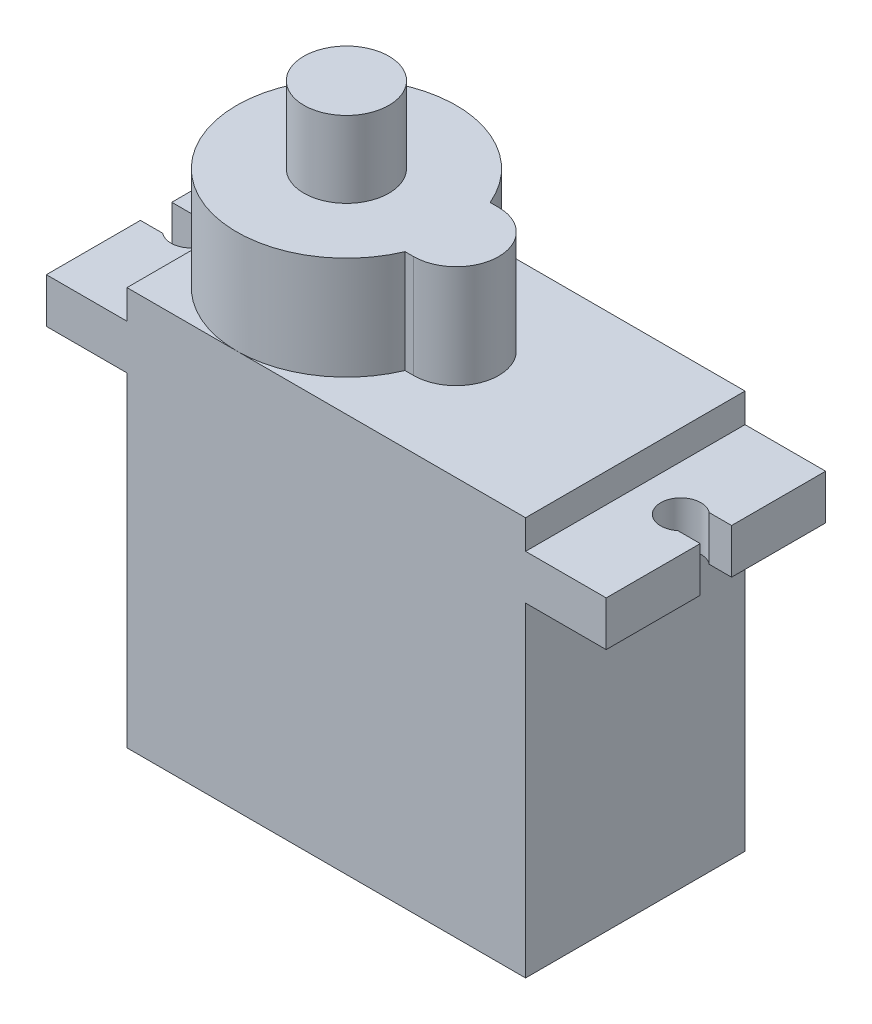
SolidWorks part; units mm, degrees
ref_plane "Front Plane" through (0, 0, 0) normal (0, 0, 1) x (1, 0, 0)
ref_plane "Top Plane" through (0, 0, 0) normal (0, 1, 0) x (1, 0, 0)
ref_plane "Right Plane" through (0, 0, 0) normal (1, 0, 0) x (0, 0, -1)
sketch "Sketch1" plane through (0, 0, 0) normal (0, 1, 0) x (1, 0, 0)
  line L1 (11.303, -6.223) -> (-11.303, -6.223)
  line L2 (11.303, -6.223) -> (11.303, 6.223)
  line L3 (11.303, 6.223) -> (-11.303, 6.223)
  line L4 (-11.303, -6.223) -> (-11.303, 6.223)
  line L5 (11.303, -6.223) -> (-11.303, 6.223) construction
  line L6 (11.303, 6.223) -> (-11.303, -6.223) construction
  point P0 (0, 0)
  dimension "D1" = 22.606
  dimension "D2" = 12.446
extrude "Boss-Extrude1" add sketch "Sketch1" along normal blind 18.415
sketch "Sketch2" plane through (0, 18.415, 0) normal (0, 1, 0) x (1, 0, 0)
  line L0 (0, 6.223) -> (-17.0969, 6.223) construction
  line L1 (11.303, 6.223) -> (-11.303, 6.223) construction
  line L2 (-11.303, 6.223) -> (-11.303, -6.223) construction
  line L3 (15.875, -6.223) -> (-15.875, -6.223)
  line L4 (15.875, -6.223) -> (15.875, 6.223) construction
  line L5 (15.875, 6.223) -> (-15.875, 6.223)
  line L6 (-15.875, -6.223) -> (-15.875, 6.223) construction
  line L7 (15.875, -6.223) -> (-15.875, 6.223) construction
  line L8 (15.875, 6.223) -> (-15.875, -6.223) construction
  line L9 (-15.875, 6.223) -> (-15.875, 0.889)
  line L10 (-15.875, 0.889) -> (-14.605, 0.889)
  line L11 (-15.875, 0) -> (-12.9515, 0) construction
  line L12 (-15.875, -0.889) -> (-14.605, -0.889)
  line L13 (-15.875, -6.223) -> (-15.875, -0.889)
  line L14 (0, 0) -> (0, 6.223) construction
  line L15 (15.875, -6.223) -> (15.875, -0.889)
  line L16 (15.875, -0.889) -> (14.605, -0.889)
  line L17 (15.875, 0.889) -> (14.605, 0.889)
  line L18 (15.875, 6.223) -> (15.875, 0.889)
  circle A0 centre (-13.8866, 0) radius 1.143 construction
  arc A1 (-14.605, 0.889) -> (-14.605, -0.889) centre (-13.8866, 0) cw
  arc A2 (14.605, 0.889) -> (14.605, -0.889) centre (13.8866, 0) ccw
  point P4 (0, 0)
  dimension "D4" = 2.286
  dimension "D1" = 4.572
  dimension "D2" = 5.334
  dimension "D3" = 1.27
extrude "Boss-Extrude2" add sketch "Sketch2" along normal blind 2.54
sketch "Sketch3" plane through (0, 20.955, 0) normal (0, 1, 0) x (1, 0, 0)
  line L0 (15.875, 6.223) -> (-15.875, 6.223) construction
  line L1 (11.303, -6.223) -> (-11.303, -6.223)
  line L2 (11.303, -6.223) -> (11.303, 6.223)
  line L3 (11.303, 6.223) -> (-11.303, 6.223)
  line L4 (-11.303, -6.223) -> (-11.303, 6.223)
  line L5 (11.303, -6.223) -> (-11.303, 6.223) construction
  line L6 (11.303, 6.223) -> (-11.303, -6.223) construction
  point P0 (0, 0)
  dimension "D1" = 22.606
extrude "Boss-Extrude3" add sketch "Sketch3" along normal blind 1.651
sketch "Sketch4" plane through (0, 22.606, 0) normal (0, 1, 0) x (1, 0, 0)
  line L0 (-5.08, -6.223) -> (-5.08, 0) construction
  line L1 (-11.303, -6.223) -> (11.303, -6.223) construction
  line L2 (-5.08, 0) -> (-11.303, 0) construction
  line L3 (-11.303, 6.223) -> (-11.303, -6.223) construction
  line L4 (1.143, 2.413) -> (0.6561, 2.413)
  line L5 (1.143, -2.413) -> (0.6561, -2.413)
  circle A0 centre (-5.08, 0) radius 6.223 construction
  circle A1 centre (1.143, 0) radius 2.413 construction
  arc A2 (0.6561, 2.413) -> (-11.303, 0) centre (-5.08, 0) ccw
  arc A3 (1.143, -2.413) -> (1.143, 2.413) centre (1.143, 0) ccw
  arc A4 (0.6561, -2.413) -> (-11.303, 0) centre (-5.08, 0) cw
  dimension "D1" = 4.826
  dimension "D2" = 12.446
  dimension "D4" = 0.4869
extrude "Boss-Extrude4" add sketch "Sketch4" along normal blind 5.842 contours A4 L5 A3 L4 A2
sketch "Sketch5" plane through (0, 28.448, 0) normal (0, 1, 0) x (1, 0, 0)
  line L0 (-5.08, 6.223) -> (-5.08, 0) construction
  line L1 (-11.303, 0) -> (-5.08, 0) construction
  arc A0 (0.6561, 2.413) -> (0.6561, -2.413) centre (-5.08, 0) ccw construction
  circle A1 centre (-5.08, 0) radius 2.413
  dimension "D1" = 4.826
extrude "Boss-Extrude5" add sketch "Sketch5" along normal blind 4.318
